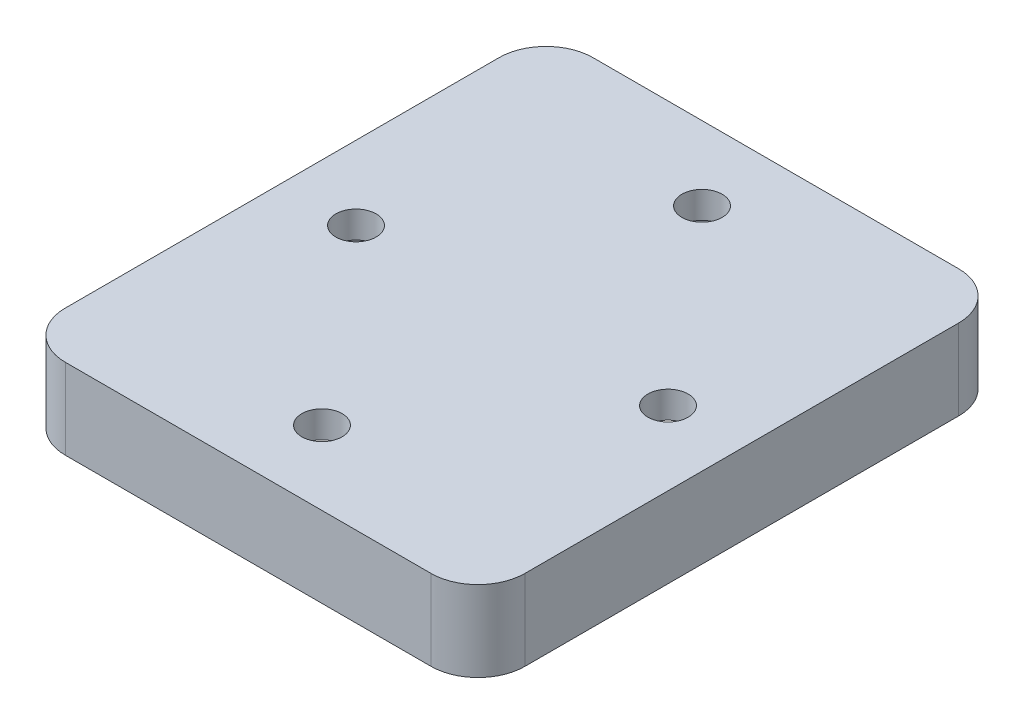
SolidWorks part; units mm, degrees
ref_plane "Front Plane" through (0, 0, 0) normal (0, 0, 1) x (1, 0, 0)
ref_plane "Top Plane" through (0, 0, 0) normal (0, 1, 0) x (1, 0, 0)
ref_plane "Right Plane" through (0, 0, 0) normal (1, 0, 0) x (0, 0, -1)
sketch "Sketch1" plane through (0, 0, 0) normal (0, 1, 0) x (1, 0, 0)
  line L4 (-7.8984, 10.0233) -> (-7.8984, -10.2967)
  line L5 (-7.8984, -10.2967) -> (7.3516, -10.2967)
  line L6 (7.3516, -0.1367) -> (7.3516, 10.0233)
  line L7 (7.3516, 10.0233) -> (-0.2734, 10.0233)
  line L8 (-15.8984, 18.0233) -> (-15.8984, -18.2967)
  line L9 (-15.8984, -18.2967) -> (15.3516, -18.2967)
  line L10 (15.3516, -18.2967) -> (15.3516, 18.0233)
  line L11 (15.3516, 18.0233) -> (-15.8984, 18.0233)
  line L12 (-0.2734, 18.0233) -> (-0.2734, 10.0233) construction
  line L13 (7.3516, -10.2967) -> (7.3516, 10.0233) construction
  line L14 (-15.8984, -0.1367) -> (-7.8984, -0.1367) construction
  line L15 (-0.2734, -10.2967) -> (-0.2734, -18.2967) construction
  line L16 (7.3516, -0.1367) -> (15.3516, -0.1367) construction
  line L17 (7.3516, 10.0233) -> (-7.8984, 10.0233) construction
  circle A0 centre (-0.2734, 14.0233) radius 1.5
  circle A1 centre (-11.8984, -0.1367) radius 1.5
  circle A2 centre (-0.2734, -14.2967) radius 1.5
  circle A3 centre (11.3516, -0.1367) radius 1.5
  point P12 (-0.2734, -0.1367)
  dimension "D2" = 3
  dimension "D1" = 8
extrude "Boss-Extrude2" add sketch "Sketch1" along normal blind 2
fillet "Fillet1" radius 2 4 edges at (-15.8984, 1, -18.0233) (-15.8984, 1, 18.2967) (15.3516, 1, 18.2967) (15.3516, 1, -18.0233)
sketch "Sketch3" plane through (0, 2, 0) normal (0, 1, 0) x (1, 0, 0)
  line L8 (13.3516, 19.5233) -> (-13.8984, 19.5233)
  line L9 (-17.3984, 16.0233) -> (-17.3984, -16.2967)
  line L10 (-13.8984, -19.7967) -> (13.3516, -19.7967)
  line L11 (16.8516, -16.2967) -> (16.8516, 16.0233)
  line L12 (13.3516, 19.5233) -> (-13.8984, 19.5233)
  line L13 (-17.3984, 16.0233) -> (-17.3984, -16.2967)
  line L14 (-13.8984, -19.7967) -> (13.3516, -19.7967)
  line L15 (16.8516, -16.2967) -> (16.8516, 16.0233)
  line L16 (13.3516, 18.0233) -> (-13.8984, 18.0233)
  line L17 (-15.8984, 16.0233) -> (-15.8984, -16.2967)
  line L18 (-13.8984, -18.2967) -> (13.3516, -18.2967)
  line L19 (15.3516, -16.2967) -> (15.3516, 16.0233)
  line L20 (13.3516, 18.0233) -> (-13.8984, 18.0233)
  line L21 (-15.8984, 16.0233) -> (-15.8984, -16.2967)
  line L22 (-13.8984, -18.2967) -> (13.3516, -18.2967)
  line L23 (15.3516, -16.2967) -> (15.3516, 16.0233)
  arc A8 (-13.8984, 19.5233) -> (-17.3984, 16.0233) centre (-13.8984, 16.0233) ccw
  arc A9 (-17.3984, -16.2967) -> (-13.8984, -19.7967) centre (-13.8984, -16.2967) ccw
  arc A10 (13.3516, -19.7967) -> (16.8516, -16.2967) centre (13.3516, -16.2967) ccw
  arc A11 (16.8516, 16.0233) -> (13.3516, 19.5233) centre (13.3516, 16.0233) ccw
  arc A12 (-13.8984, 19.5233) -> (-17.3984, 16.0233) centre (-13.8984, 16.0233) ccw
  arc A13 (-17.3984, -16.2967) -> (-13.8984, -19.7967) centre (-13.8984, -16.2967) ccw
  arc A14 (13.3516, -19.7967) -> (16.8516, -16.2967) centre (13.3516, -16.2967) ccw
  arc A15 (16.8516, 16.0233) -> (13.3516, 19.5233) centre (13.3516, 16.0233) ccw
  arc A16 (-13.8984, 18.0233) -> (-15.8984, 16.0233) centre (-13.8984, 16.0233) ccw
  arc A17 (-15.8984, -16.2967) -> (-13.8984, -18.2967) centre (-13.8984, -16.2967) ccw
  arc A18 (13.3516, -18.2967) -> (15.3516, -16.2967) centre (13.3516, -16.2967) ccw
  arc A19 (15.3516, 16.0233) -> (13.3516, 18.0233) centre (13.3516, 16.0233) ccw
  arc A20 (-13.8984, 18.0233) -> (-15.8984, 16.0233) centre (-13.8984, 16.0233) ccw
  arc A21 (-15.8984, -16.2967) -> (-13.8984, -18.2967) centre (-13.8984, -16.2967) ccw
  arc A22 (13.3516, -18.2967) -> (15.3516, -16.2967) centre (13.3516, -16.2967) ccw
  arc A23 (15.3516, 16.0233) -> (13.3516, 18.0233) centre (13.3516, 16.0233) ccw
  dimension "D1" = 1.5
  dimension "D2" = 0
extrude "Boss-Extrude3" add sketch "Sketch3" against normal blind 6
